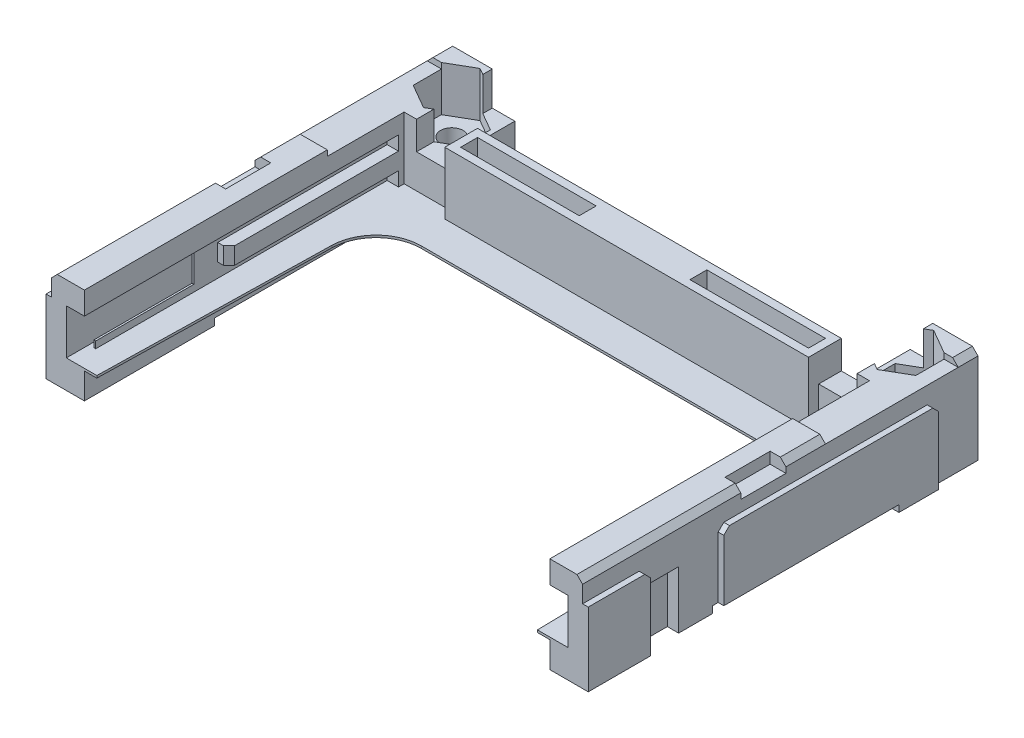
SolidWorks part; units mm, degrees
ref_plane "Alzado" through (0, 0, 0) normal (0, 0, 1) x (1, 0, 0)
ref_plane "Planta" through (0, 0, 0) normal (0, 1, 0) x (1, 0, 0)
ref_plane "Vista lateral" through (0, 0, 0) normal (1, 0, 0) x (0, 0, -1)
sketch "Croquis1" plane through (0, 0, 0) normal (0, 1, 0) x (1, 0, 0)
  line L0 (23.5, 0) -> (-23.5, 0)
  line L1 (-23.5, 0) -> (-23.5, -35)
  line L2 (-23.5, -35) -> (-20.6, -35)
  line L3 (-20.6, -35) -> (-20.6, -6.7)
  line L4 (-20.6, -6.7) -> (20.6, -6.7)
  line L5 (0, 0) -> (0, -27.1659) construction
  line L6 (20.6, -35) -> (20.6, -6.7)
  line L7 (23.5, -35) -> (20.6, -35)
  line L8 (23.5, 0) -> (23.5, -35)
  point P9 (0, -6.7)
  dimension "D1" = 23.5
  dimension "D2" = 35
  dimension "D3" = 6.7
  dimension "D4" = 2.9
extrude "Extruir1" add sketch "Croquis1" along normal blind 9.9
sketch "Croquis2" plane through (0, 9.9, 0) normal (0, 1, 0) x (-1, 0, 0)
  line L2 (-23.5, 0) -> (23.5, 0) construction
  circle A0 centre (-20.08, 3) radius 1
  circle A1 centre (20.08, 3) radius 1
  dimension "D1" = 2
  dimension "D2" = 2
  dimension "D3" = 3
  dimension "D4" = 40.16
  dimension "D5" = 20.08
extrude "Cortar-Extruir1" cut sketch "Croquis2" against normal blind 15.9
sketch "Croquis3" plane through (0, 9.9, 0) normal (0, 1, 0) x (-1, 0, 0)
  line L1 (-20.08, 5.5) -> (-22.2451, 4.25)
  line L2 (-22.2451, 4.25) -> (-22.2451, 1.75)
  line L3 (-22.2451, 1.75) -> (-20.08, 0.5)
  line L4 (-20.08, 0.5) -> (-17.9149, 1.75)
  line L5 (-17.9149, 1.75) -> (-17.9149, 4.25)
  line L6 (-17.9149, 4.25) -> (-20.08, 5.5)
  line L7 (20.08, 5.5) -> (17.9149, 4.25)
  line L8 (17.9149, 4.25) -> (17.9149, 1.75)
  line L9 (17.9149, 1.75) -> (20.08, 0.5)
  line L10 (20.08, 0.5) -> (22.2451, 1.75)
  line L11 (22.2451, 1.75) -> (22.2451, 4.25)
  line L12 (22.2451, 4.25) -> (20.08, 5.5)
  circle A0 centre (-20.08, 3) radius 2.5 construction
  circle A1 centre (20.08, 3) radius 2.5 construction
extrude "Cortar-Extruir2" cut sketch "Croquis3" against normal blind 4
sketch "Croquis4" plane through (0, 9.9, 0) normal (0, 1, 0) x (-1, 0, 0)
  line L0 (-23.5, 0) -> (23.5, 0) construction
  line L1 (-17.5, -1.2275) -> (17.5, -1.2275)
  line L2 (-17.5, -1.2275) -> (-17.5, 1.5)
  line L3 (-17.5, 1.5) -> (17.5, 1.5)
  line L4 (17.5, -1.2275) -> (17.5, 1.5)
  dimension "D1" = 35
  dimension "D2" = 17.5
  dimension "D3" = 1.5
extrude "Cortar-Extruir3" cut sketch "Croquis4" against normal blind 24
sketch "Croquis5" plane through (0, 9.9, 0) normal (0, 1, 0) x (-1, 0, 0)
  line L0 (20.6, 6.7) -> (-20.6, 6.7) construction
  line L1 (-17.5, 1.5) -> (17.5, 1.5)
  line L2 (-17.5, 1.5) -> (-17.5, 4.7)
  line L3 (-17.5, 4.7) -> (17.5, 4.7)
  line L4 (17.5, 1.5) -> (17.5, 4.7)
  dimension "D1" = 2
extrude "Cortar-Extruir4" cut sketch "Croquis5" against normal blind 8.5
sketch "Croquis6" plane through (0, 9.9, 0) normal (0, 1, 0) x (-1, 0, 0)
  line L1 (-19.5, -1.8381) -> (19.5, -1.8381)
  line L2 (-19.5, -1.8381) -> (-19.5, 12.6146)
  line L3 (-19.5, 12.6146) -> (19.5, 12.6146)
  line L4 (19.5, -1.8381) -> (19.5, 12.6146)
  dimension "D1" = 39
  dimension "D2" = 19.5
extrude "Cortar-Extruir5" cut sketch "Croquis6" against normal blind 3
ref_plane "Plano1" through (0, 3.9, 0) normal (0, 1, 0) x (-1, 0, 0)
sketch "Croquis7" plane through (0, 3.9, 0) normal (0, 1, 0) x (-1, 0, 0)
  line L0 (-20.6, 35) -> (-19.5, 35)
  line L1 (-19.5, 35) -> (-19.0806, 14.6177)
  line L2 (-15.0815, 10.7) -> (15.0815, 10.7)
  line L3 (0, 10.7) -> (0, 23.1693) construction
  line L4 (-19.5, 6.7) -> (19.5, 6.7) construction
  line L5 (20.6, 6.7) -> (-20.6, 6.7)
  line L6 (-20.6, 6.7) -> (-20.6, 35)
  line L7 (17.5, 4.7) -> (-17.5, 4.7) construction
  line L8 (-23.5, 35) -> (-23.5, 0) construction
  line L9 (20.6, 6.7) -> (20.6, 35)
  line L10 (19.5, 35) -> (19.0806, 14.6177)
  line L11 (20.6, 35) -> (19.5, 35)
  arc A0 (-19.0806, 14.6177) -> (-15.0815, 10.7) centre (-15.0815, 14.7) ccw
  arc A1 (19.0806, 14.6177) -> (15.0815, 10.7) centre (15.0815, 14.7) cw
  point P16 (-19, 10.7)
  point P24 (0, 6.7)
  dimension "D4" = 4
  dimension "D1" = 6
  dimension "D2" = 4
  dimension "D3" = 4.5
extrude "Extruir2" add sketch "Croquis7" against normal blind 0.2
sketch "Croquis8" plane through (0, 9.9, 0) normal (0, 1, 0) x (-1, 0, 0)
  line L0 (-20.6, 35) -> (-23.5, 35) construction
  line L1 (-24.6311, 1.75) -> (24.9421, 1.75)
  line L2 (-24.6311, 1.75) -> (-24.6311, 13.5)
  line L3 (-24.6311, 13.5) -> (24.9421, 13.5)
  line L4 (24.9421, 1.75) -> (24.9421, 13.5)
  dimension "D1" = 21.5
extrude "Cortar-Extruir6" cut sketch "Croquis8" against normal blind 0.5
sketch "Croquis9" plane through (0, 9.9, 0) normal (0, 1, 0) x (-1, 0, 0)
  line L0 (20.6, 35) -> (20.6, 13.5) construction
  line L1 (24.5603, 17) -> (22.1, 17)
  line L2 (24.5603, 17) -> (24.5603, 21)
  line L3 (24.5603, 21) -> (22.1, 21)
  line L4 (22.1, 17) -> (22.1, 21)
  line L5 (23.5, 35) -> (20.6, 35) construction
  line L6 (0, 0) -> (0, -15.5719) construction
  line L7 (-22.1, 17) -> (-22.1, 21)
  line L8 (-24.5603, 21) -> (-22.1, 21)
  line L9 (-24.5603, 17) -> (-24.5603, 21)
  line L10 (-24.5603, 17) -> (-22.1, 17)
  dimension "D1" = 1.5
  dimension "D2" = 14
  dimension "D3" = 18
extrude "Cortar-Extruir7" cut sketch "Croquis9" against normal blind 1
chamfer "Chaflán1" distance 0.5 angle 45 4 edges at (23.5, 9.9, 15.25) (23.5, 9.9, 28) (-23.5, 9.9, 28) (-23.5, 9.9, 15.25)
chamfer "Chaflán2" distance 0.5 angle 45 2 edges at (23.5, 9.9, 0.875) (-23.5, 9.9, 0.875)
sketch "Croquis10" plane through (0, 9.4, 0) normal (0, 1, 0) x (-1, 0, 0)
  line L0 (17.5, 4.7) -> (-17.5, 4.7) construction
  line L1 (-16.1, 4.7) -> (16.1, 4.7)
  line L2 (-16.1, 4.7) -> (-16.1, 7.6)
  line L3 (-16.1, 7.6) -> (16.1, 7.6)
  line L4 (16.1, 4.7) -> (16.1, 7.6)
  dimension "D1" = 32.2
  dimension "D2" = 2.9
  dimension "D3" = 16.1
extrude "Extruir3" add sketch "Croquis10" against normal up to surface (5.5 mm away) up to face at (0, 3.9, 20.2403)
sketch "Croquis11" plane through (0, 9.4, 0) normal (0, 1, 0) x (-1, 0, 0)
  line L0 (-16.1, 4.7) -> (16.1, 4.7) construction
  line L1 (-15.4, 5.4) -> (-4.9, 5.4)
  line L2 (-15.4, 5.4) -> (-15.4, 6.9)
  line L3 (-15.4, 6.9) -> (-4.9, 6.9)
  line L4 (-4.9, 5.4) -> (-4.9, 6.9)
  line L5 (-16.1, 7.6) -> (-16.1, 4.7) construction
  line L6 (16.1, 7.6) -> (-16.1, 7.6) construction
  line L7 (0, 0) -> (0, -6.0247) construction
  line L8 (4.9, 5.4) -> (4.9, 6.9)
  line L9 (15.4, 6.9) -> (4.9, 6.9)
  line L10 (15.4, 5.4) -> (15.4, 6.9)
  line L11 (15.4, 5.4) -> (4.9, 5.4)
  point P6 (-16.1, 6.15)
  dimension "D1" = 0.7
  dimension "D2" = 0.7
  dimension "D3" = 0.7
  dimension "D4" = 10.5
extrude "Cortar-Extruir8" cut sketch "Croquis11" against normal blind 2.5
sketch "Croquis12" plane through (-23.5, 0, 0) normal (-1, 0, 0) x (0, 0, 1)
  line L0 (0, 0) -> (35, 0) construction
  line L1 (7.5, 2) -> (23.5, 2)
  line L2 (7.5, 2) -> (7.5, 0)
  line L3 (7.5, 0) -> (23.5, 0)
  line L4 (23.5, 2) -> (23.5, 0)
  line L5 (0, 9.4) -> (0, 0) construction
  dimension "D1" = 7.5
  dimension "D2" = 23.5
  dimension "D3" = 2
extrude "Cortar-Extruir9" cut sketch "Croquis12" against normal blind 57.5
sketch "Croquis13" plane through (0, 0, 0) normal (0, -1, 0) x (1, 0, 0)
  line L1 (17.5, 1.5) -> (-17.5, 1.5)
  line L2 (17.5, 1.5) -> (17.5, 4.7)
  line L3 (17.5, 4.7) -> (-17.5, 4.7)
  line L4 (-17.5, 1.5) -> (-17.5, 4.7)
  line L5 (-20.6, 6.7) -> (20.6, 6.7) construction
  dimension "D1" = 2
extrude "Cortar-Extruir10" cut sketch "Croquis13" against normal blind 0.7
sketch "Croquis15" plane through (-23.5, 0, 0) normal (-1, 0, 0) x (0, 0, 1)
  line L0 (4, 0) -> (4, 7.9)
  line L1 (0, 0) -> (7.5, 0) construction
  line L2 (4, 7.9) -> (23, 7.9)
  line L3 (23, 7.9) -> (23, 2)
  line L4 (23.5, 2) -> (7.5, 2) construction
  line L5 (23, 2) -> (7.5, 2)
  line L6 (7.5, 2) -> (7.5, 0)
  line L7 (7.5, 0) -> (4, 0)
  line L8 (35, 7.9) -> (29.5, 7.9)
  line L9 (35, 9.4) -> (35, 0) construction
  line L10 (29.5, 7.9) -> (29.5, 0)
  line L11 (23.5, 0) -> (35, 0) construction
  line L12 (29.5, 0) -> (35, 0)
  line L13 (35, 0) -> (35, 7.9)
  line L14 (0, 9.4) -> (0, 0) construction
  line L15 (13.5, 9.9) -> (17, 9.9) construction
  dimension "D1" = 4
  dimension "D2" = 19
  dimension "D3" = 2
  dimension "D4" = 5.5
extrude "Extruir4" add sketch "Croquis15" along normal blind 0.5
chamfer "Chaflán3" distance 0.5 angle 45 3 edges at (-23.75, 7.9, 29.5) (-23.75, 7.9, 23) (-23.75, 7.9, 4)
sketch "Croquis16" plane through (-23.5, 0, 0) normal (-1, 0, 0) x (0, 0, 1)
  line L0 (23.5, 0) -> (29.5, 0) construction
  line L1 (29.5, 0) -> (26.5, 0)
  line L2 (29.5, 0) -> (29.5, 6.5)
  line L3 (29.5, 6.5) -> (26.5, 6.5)
  line L4 (26.5, 0) -> (26.5, 6.5)
  dimension "D1" = 3
  dimension "D2" = 6.5
extrude "Cortar-Extruir11" cut sketch "Croquis16" against normal blind 1
mirror "Simetría1" about plane through (0, 0, 0) normal (1, 0, 0) of "Cortar-Extruir11", "Extruir4"
chamfer "Chaflán4" distance 0.5 angle 45 3 edges at (23.75, 7.9, 4) (23.75, 7.9, 23) (23.75, 7.9, 29.5)
sketch "Croquis17" plane through (-20.6, 0, 0) normal (1, 0, 0) x (0, 0, -1)
  line L0 (-35, 7.9) -> (-7.2, 7.9)
  line L1 (-35, 9.9) -> (-35, 3.9) construction
  line L2 (-7.2, 7.9) -> (-7.2, 6.65)
  line L3 (-7.2, 6.65) -> (-22.2, 6.65)
  line L4 (-22.2, 6.65) -> (-22.2, 5.15)
  line L5 (-22.2, 5.15) -> (-7.2, 5.15)
  line L6 (-7.2, 5.15) -> (-7.2, 3.9)
  line L7 (-6.7, 3.9) -> (-35, 3.9) construction
  line L8 (-7.2, 3.9) -> (-35, 3.9)
  line L9 (-35, 3.9) -> (-35, 7.9)
  line L10 (-35, 9.9) -> (-13.5, 9.9) construction
  dimension "D1" = 27.8
  dimension "D2" = 27.8
  dimension "D3" = 2
  dimension "D4" = 1.5
  dimension "D5" = 1.25
  dimension "D6" = 15
extrude "Cortar-Extruir12" cut sketch "Croquis17" against normal blind 1
chamfer "Chaflán5" distance 0.5 angle 45 1 edges at (-20.6, 5.9, 22.2)
mirror "Simetría2" about plane through (0, 0, 0) normal (1, 0, 0) of "Cortar-Extruir12"
chamfer "Chaflán6" distance 0.5 angle 45 1 edges at (20.6, 5.9, 22.2)
sketch "Croquis18" plane through (0, 0, 35) normal (0, 0, 1) x (1, 0, 0)
  line L0 (-20.6, 9.9) -> (-20.6, 7.9) construction
  line L1 (-21.7601, 7.9) -> (-22.2, 7.9)
  line L2 (-21.7601, 7.9) -> (-21.7601, 3.9)
  line L3 (-21.7601, 3.9) -> (-22.2, 3.9)
  line L4 (-22.2, 7.9) -> (-22.2, 3.9)
  line L5 (0, 0) -> (0, -5.8288) construction
  line L6 (22.2, 7.9) -> (22.2, 3.9)
  line L7 (21.7601, 3.9) -> (22.2, 3.9)
  line L8 (21.7601, 7.9) -> (21.7601, 3.9)
  line L9 (21.7601, 7.9) -> (22.2, 7.9)
  point P4 (-20.6, 8.9)
  dimension "D1" = 1.6
extrude "Cortar-Extruir13" cut sketch "Croquis18" against normal blind 22
sketch "Croquis19" plane through (-21.6, 0, 0) normal (1, 0, 0) x (0, 0, -1)
  line L0 (-35, 7.9) -> (-35, 3.9) construction
  line L1 (-35, 7.3) -> (-24.304, 7.3)
  line L2 (-35, 7.3) -> (-35, 4.5)
  line L3 (-35, 4.5) -> (-24.304, 4.5)
  line L4 (-24.304, 7.3) -> (-24.304, 4.5)
  line L5 (-35, 3.9) -> (-7.2, 3.9) construction
  line L6 (-7.2, 7.9) -> (-35, 7.9) construction
  dimension "D1" = 0.6
  dimension "D2" = 0.6
extrude "Cortar-Extruir14" cut sketch "Croquis19" against normal blind 0.2
sketch "Croquis20" plane through (-21.6, 0, 0) normal (1, 0, 0) x (0, 0, -1)
  line L0 (-7.2, 7.9) -> (-35, 7.9) construction
  line L1 (-35, 3.9) -> (-33, 3.9)
  line L2 (-35, 3.9) -> (-35, 7.9)
  line L3 (-35, 7.9) -> (-33, 7.9)
  line L4 (-33, 3.9) -> (-33, 7.9)
  dimension "D1" = 2
extrude "Cortar-Extruir15" cut sketch "Croquis20" against normal blind 0.2
mirror "Simetría3" about plane through (0, 0, 0) normal (1, 0, 0) of "Cortar-Extruir15", "Cortar-Extruir14"
sketch "Croquis21" plane through (24, 0, 0) normal (1, 0, 0) x (0, 0, -1)
  line L0 (-35, 9.9) -> (-21, 9.9) construction
  line L1 (4.3652, -1.6674) -> (-38.5, -1.6674)
  line L2 (4.3652, -1.6674) -> (4.3652, 1.4)
  line L3 (4.3652, 1.4) -> (-38.5, 1.4)
  line L4 (-38.5, -1.6674) -> (-38.5, 1.4)
  dimension "D1" = 8.5
extrude "Cortar-Extruir16" cut sketch "Croquis21" against normal blind 58
